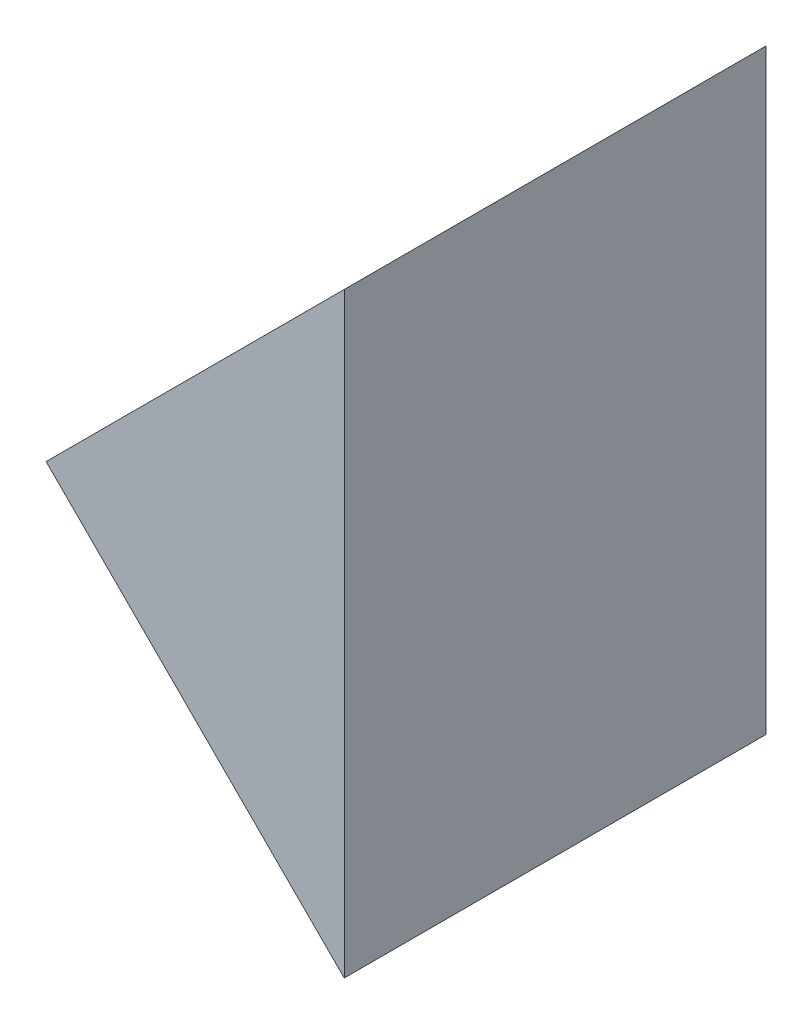
SolidWorks part; units mm, degrees
ref_plane "前视基准面" through (0, 0, 0) normal (0, 0, 1) x (1, 0, 0)
ref_plane "上视基准面" through (0, 0, 0) normal (0, 1, 0) x (1, 0, 0)
ref_plane "右视基准面" through (0, 0, 0) normal (1, 0, 0) x (0, 0, -1)
sketch "草图1" plane through (0, 0, 0) normal (0, 0, 1) x (1, 0, 0)
  line L0 (196.7073, 60.0611) -> (182.5652, 45.919)
  line L1 (182.5652, 45.919) -> (196.7073, 31.7768)
  line L2 (196.7073, 31.7768) -> (196.7073, 60.0611)
  dimension "D1" = 20
  dimension "D2" = 20
extrude "凸台-拉伸1" add sketch "草图1" along normal blind 20
